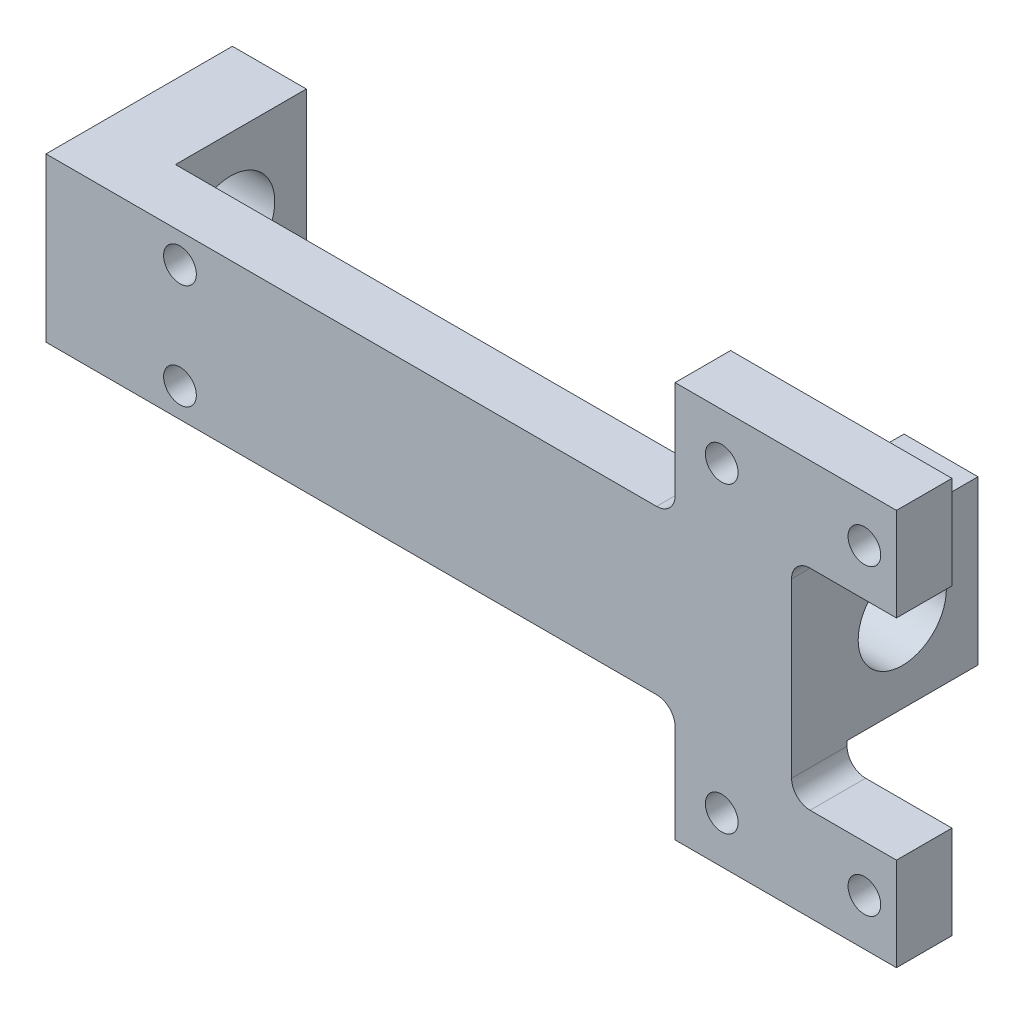
SolidWorks part; units mm, degrees
material "6061-T6 (SS)"
ref_plane "Front Plane" through (0, 0, 0) normal (0, 0, 1) x (1, 0, 0)
ref_plane "Top Plane" through (0, 0, 0) normal (0, 1, 0) x (1, 0, 0)
ref_plane "Right Plane" through (0, 0, 0) normal (1, 0, 0) x (0, 0, -1)
sketch "Sketch1" plane through (0, 0, 0) normal (1, 0, 0) x (0, 0, -1)
  line L0 (-19, 14) -> (-19, -14)
  line L1 (-19, -14) -> (13, -14)
  line L2 (-7.5692, 11.8266) -> (-7.5692, -6.597) construction
  line L3 (13, 14) -> (-19, 14)
  line L4 (13, -14) -> (13, 14)
  line L6 (0, 0) -> (29.5705, 0) construction
  line L7 (0, 0) -> (0, -32.9228) construction
  circle A0 centre (0, 0) radius 7.5692
  point P8 (13, 0)
  dimension "D1" = 15.1384
  dimension "D2" = 19
  dimension "D3" = 28
  dimension "D4" = 13
extrude "Boss-Extrude1" add sketch "Sketch1" along normal mid plane 128
sketch "Sketch5" plane through (0, 0, 0) normal (0, 0, 1) x (1, 0, 0)
  line L0 (64, 14) -> (-64, 14) construction
  line L1 (-51.3, -14) -> (51.3, -14)
  line L2 (-51.3, -14) -> (-51.3, 14)
  line L3 (-51.3, 14) -> (51.3, 14)
  line L4 (51.3, -14) -> (51.3, 14)
  line L5 (-51.3, -14) -> (51.3, 14) construction
  line L6 (-51.3, 14) -> (51.3, -14) construction
  line L7 (64, 14) -> (64, -14) construction
  point P0 (0, 0)
  dimension "D1" = 12.7
extrude "Cut-Extrude1" cut sketch "Sketch5" against normal blind 33.147 and the other way offset from surface (9.475 mm away) 9.525 other way up to face at (0, 0, 19)
sketch "Sketch6" plane through (0, 0, 9.475) normal (0, 0, -1) x (-1, 0, 0)
  line L1 (41, -9) -> (-41, -9)
  line L2 (41, -9) -> (41, 9)
  line L3 (41, 9) -> (-41, 9)
  line L4 (-41, -9) -> (-41, 9)
  line L5 (41, -9) -> (-41, 9) construction
  line L6 (41, 9) -> (-41, -9) construction
  point P0 (0, 0)
  dimension "D1" = 82
  dimension "D2" = 18
hole_wizard "#10 Clearance Hole1" positions "Sketch4" profile "Sketch3" hole size "#10" standard "ANSI Inch"
sketch "Sketch4" plane through (-39.5579, -3.6708, 9.475) normal (0, 0, -1) x (-1, 0, 0)
  line L0 (-39.5579, 3.6708) -> (-39.5579, 12.3399) construction
  line L1 (-39.5579, 3.6708) -> (27.2845, 3.6708) construction
  point P32 (1.4421, -5.3292)
  point P35 (1.4421, 12.6708)
sketch "Sketch3" plane through (-41, -9, 9.475) normal (1, 0, 0) x (0, 1, 0)
  line L0 (0, 0) -> (0, 27.0864)
  line L1 (0, 27.0864) -> (2.8067, 25.4)
  line L2 (2.8067, 25.4) -> (2.8067, 0)
  line L5 (2.8067, 0) -> (0, 0)
  line L10 (0, 27.0864) -> (-2.8067, 25.4) construction
  line L11 (0, -6.35) -> (0, 107.95) construction
  dimension "Hole Dia." = 5.6134
  dimension "Hole Depth" = 25.4
  dimension "Drill Angle" = 118
sketch "Sketch7" plane through (0, 0, 9.475) normal (0, 0, -1) x (-1, 0, 0)
  line L0 (-51.3, -14) -> (51.3, -14) construction
  line L1 (-44, -14) -> (-64, -14)
  line L2 (-44, -14) -> (-44, -34)
  line L3 (-44, -34) -> (-82, -34)
  line L4 (-82, -18) -> (-82, -34)
  line L5 (-64, -14) -> (-64, -18)
  line L6 (-64, -18) -> (-82, -18)
  dimension "D1" = 18
  dimension "D2" = 20
  dimension "D3" = 4
  dimension "D4" = 16
extrude "Boss-Extrude2" add sketch "Sketch7" against normal up to surface (9.525 mm away) up to face at (-43.8067, -9, 19)
hole_wizard "#10 Clearance Hole2" positions "Sketch10" profile "Sketch9" hole size "#10" standard "ANSI Inch" end condition through all
sketch "Sketch10" plane through (0, 0, 9.475) normal (0, 0, -1) x (-1, 0, 0)
  line L1 (-82, -34) -> (-44, -34) construction
  line L2 (-64, -18) -> (-82, -18) construction
  line L3 (-44, -34) -> (-44, -14) construction
  line L4 (-82, -18) -> (-82, -34) construction
  circle A0 centre (-76.5, -26) radius 8 construction
  circle A1 centre (-52, -26) radius 8 construction
  point P0 (-76.5, -26)
  point P4 (-52, -26)
  dimension "D1" = 5.5
sketch "Sketch9" plane through (76.5, -26, 9.475) normal (1, 0, 0) x (0, 1, 0)
  line L0 (0, 0) -> (0, 9.5251)
  line L1 (0, 9.5251) -> (2.8067, 9.5251)
  line L2 (2.8067, 9.5251) -> (2.8067, 0)
  line L5 (2.8067, 0) -> (0, 0)
  line L11 (0, -6.35) -> (0, 107.95) construction
  dimension "Thru Hole Dia." = 5.6134
  dimension "Thru Hole Depth" = 9.5251
mirror "Mirror2" about plane through (0, 0, 0) normal (0, 1, 0) of "#10 Clearance Hole2", "Boss-Extrude2"
fillet "Fillet2" radius 3.175 4 edges at (64, 18, 14.2375) (64, -18, 14.2375)
